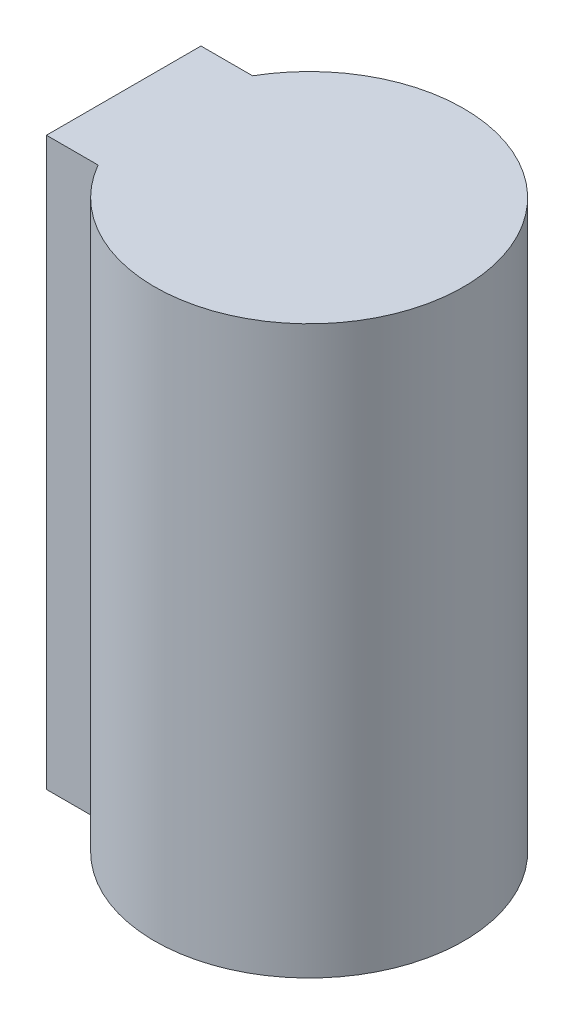
SolidWorks part; units mm, degrees
material "1060 Legierung"
ref_plane "Ebene vorne" through (0, 0, 0) normal (0, 0, 1) x (1, 0, 0)
ref_plane "Ebene oben" through (0, 0, 0) normal (0, 1, 0) x (1, 0, 0)
ref_plane "Ebene rechts" through (0, 0, 0) normal (1, 0, 0) x (0, 0, -1)
sketch "Skizze1" plane through (0, 0, 0) normal (0, 1, 0) x (1, 0, 0)
  line L0 (-36, 15) -> (-36, -15)
  line L1 (-36, 15) -> (-25.9808, 15)
  line L2 (-36, -15) -> (-25.9808, -15)
  arc A0 (-25.9808, -15) -> (-25.9808, 15) centre (0, 0) ccw
  point P18 (28.6891, 8.7712)
  point P20 (24, 0)
  dimension "D1" = 60
  dimension "D2" = 36
  dimension "D4" = 30
extrude "Basis" add sketch "Skizze1" along normal blind 110
